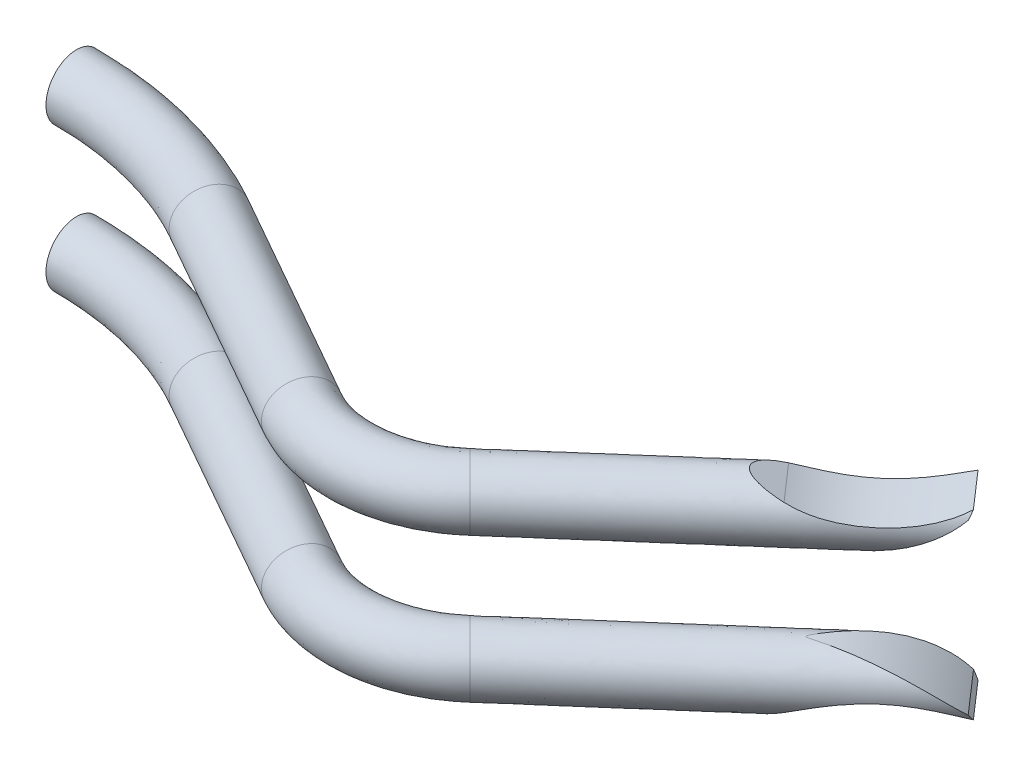
SolidWorks part; units mm, degrees
ref_plane "Front Plane" through (0, 0, 0) normal (0, 0, 1) x (1, 0, 0)
ref_plane "Top Plane" through (0, 0, 0) normal (0, 1, 0) x (1, 0, 0)
ref_plane "Right Plane" through (0, 0, 0) normal (1, 0, 0) x (0, 0, -1)
sketch "linear trace" plane through (0, 0, 0) normal (0, 1, 0) x (1, 0, 0)
  line L0 (544, 1224) -> (2720, 1224) construction
  line L1 (58.6476, 31.614) -> (61.5916, 29.9464)
  line L2 (67.5367, 33.5179) -> (63.697, 30.1609)
  line L3 (56.1008, 32.2852) -> (31.8502, 32.2852)
  line L4 (31.8502, 32.2852) -> (11.5916, 32.2852)
  line L8 (11.5916, 32.2852) -> (-52.4084, 32.2852)
  line L9 (61.5916, 31.5379) -> (61.5916, 26.5009) construction
  line L10 (58.6476, 34.5776) -> (58.6476, 27.8816) construction
  line L11 (31.8502, 35.1699) -> (31.8502, 28.7738) construction
  line L12 (66.6219, 34.4328) -> (68.5343, 32.5203) construction
  line L13 (11.5916, 37.7013) -> (11.5916, 27.1178) construction
  line L14 (-20.4084, 37.7013) -> (-20.4084, 23.3633) construction
  line L15 (56.1008, 34.5776) -> (56.1008, 28.9762) construction
  line L16 (-52.4084, 37.7013) -> (-52.4084, 27.1178) construction
  line L17 (-72.6669, 32.2852) -> (-52.4084, 32.2852)
  line L18 (-72.6669, 35.1699) -> (-72.6669, 28.7738) construction
  line L19 (-96.9175, 32.2852) -> (-72.6669, 32.2852)
  line L20 (-96.9175, 34.5776) -> (-96.9175, 28.9762) construction
  arc A0 (61.5916, 29.9464) -> (63.697, 30.1609) centre (62.4931, 31.5379) ccw
  arc A1 (56.1008, 32.2852) -> (58.6476, 31.614) centre (56.1008, 27.1178) cw
  point P27 (-20.4084, 32.2852)
ref_plane "Plane1" through (61.5916, 0, 0) normal (1, 0, 0) x (0, 0, -1)
ref_plane "Plane2" through (58.6476, 0, 0) normal (1, 0, 0) x (0, 0, -1)
ref_plane "Plane3" through (31.8502, 0, 0) normal (1, 0, 0) x (0, 0, -1)
ref_plane "Plane4" through (50.5273, 0, -50.5273) normal (0.7071, 0, -0.7071) x (0.7071, 0, 0.7071)
sketch "Sketch2" plane through (50.5273, 0, -50.5273) normal (0.7071, 0, -0.7071) x (0.7071, 0, 0.7071)
  circle A0 centre (24.0549, 0) radius 0.425
  point P4 (24.0549, 0)
  dimension "D1" = 0.85
sketch "Sketch3" plane through (61.5916, 0, 0) normal (1, 0, 0) x (0, 0, -1)
  circle A0 centre (29.9464, 0) radius 0.5
  dimension "D1" = 1
sketch "Sketch4" plane through (0, 0, 0) normal (0, 1, 0) x (1, 0, 0)
  line L2 (67.5367, 33.5179) -> (63.697, 30.1609) construction
  line L3 (67.5367, 33.5179) -> (63.697, 30.1609)
  line L4 (58.6476, 31.614) -> (61.5916, 29.9464) construction
  line L5 (58.6476, 31.614) -> (61.5916, 29.9464)
  arc A0 (61.5916, 29.9464) -> (63.697, 30.1609) centre (62.4931, 31.5379) ccw construction
  arc A1 (61.5916, 29.9464) -> (63.697, 30.1609) centre (62.4931, 31.5379) ccw
  arc A2 (58.6476, 31.614) -> (56.1008, 32.2852) centre (56.1008, 27.1178) ccw construction
  arc A3 (58.6476, 31.614) -> (56.1008, 32.2852) centre (56.1008, 27.1178) ccw
sweep "Sweep4" add profiles "Sketch2" path "Sketch4"
sketch "Sketch6" plane through (0, 0, 0) normal (0, 1, 0) x (1, 0, 0)
  line L0 (56.1008, 32.2852) -> (31.8502, 32.2852) construction
  line L1 (56.1008, 32.2852) -> (31.8502, 32.2852)
  line L2 (56.1008, 32.2852) -> (56.1008, 31.7852)
  line L3 (31.8502, 35.1699) -> (31.8502, 28.7738) construction
  line L4 (31.8502, 35.1699) -> (31.8502, 28.7738) construction
  line L5 (31.8502, 31.0852) -> (56.1008, 31.7852)
  line L6 (31.8502, 31.0852) -> (31.8502, 30.4852)
  line L7 (31.8502, 30.4852) -> (11.5916, 30.2852)
  line L8 (11.5916, 30.2852) -> (11.5916, 29.7852)
  line L9 (11.5916, 29.7852) -> (-52.4084, 29.7852)
  line L11 (11.5916, 32.2852) -> (-52.4084, 32.2852) construction
  line L15 (31.8502, 32.2852) -> (11.5916, 32.2852) construction
  line L17 (11.5916, 32.2852) -> (-52.4084, 32.2852)
  line L18 (-20.4084, 32.2852) -> (-20.4084, 29.7852) construction
  line L19 (31.8502, 32.2852) -> (11.5916, 32.2852)
  line L20 (11.5916, 32.2852) -> (11.5916, 27.6338) construction
  line L21 (-20.4084, 37.7013) -> (-20.4084, 23.3633) construction
  line L22 (-52.4084, 32.2852) -> (-52.4084, 27.6338) construction
  line L23 (-72.6669, 35.1699) -> (-72.6669, 28.7738) construction
  line L24 (-72.6669, 32.2852) -> (-52.4084, 32.2852)
  line L25 (-52.4084, 30.2852) -> (-52.4084, 29.7852)
  line L26 (-72.6669, 30.4852) -> (-52.4084, 30.2852)
  line L27 (-72.6669, 31.0852) -> (-72.6669, 30.4852)
  line L28 (-72.6669, 31.0852) -> (-96.9175, 31.7852)
  line L29 (-96.9175, 32.2852) -> (-96.9175, 31.7852)
  line L30 (-96.9175, 32.2852) -> (-72.6669, 32.2852)
  dimension "D1" = 0.5
  dimension "D2" = 1.2
  dimension "D3" = 2
  dimension "D4" = 1.8
  dimension "D5" = 2.5
revolve "Revolve1" [suppressed] add sketch "Sketch6" angle 360 about L8
ref_plane "Plane5" through (12.6499, 0, 14.4689) normal (-0.6582, 0, -0.7528) x (-0.7528, 0, 0.6582)
ref_plane "Plane6" through (12.979, 0, 14.8453) normal (-0.6582, 0, -0.7528) x (-0.7528, 0, 0.6582)
sketch "Sketch7" plane through (12.979, 0, 14.8453) normal (-0.6582, 0, -0.7528) x (-0.7528, 0, 0.6582)
  line L0 (804.1764, 1008.5492) -> (2890.5681, 390.5318) construction
  line L1 (-70.9069, -0.2587) -> (-70.4249, -0.4803)
  line L2 (-72.7165, -0.1669) -> (-72.7639, -0.2587)
  line L3 (-71.0972, 0.425) -> (-67.8057, 0.425) construction
  line L4 (-71.0972, 0.425) -> (-73.643, 0.425)
  line L5 (-73.643, 0.425) -> (-73.1771, -0.8091)
  line L6 (-73.1771, -0.8091) -> (-70.4249, -0.4803)
  line L7 (-67.8057, 0.425) -> (-72.906, 0.425) construction
  line L8 (-67.8057, 0.425) -> (-73.643, 0.425) construction
  arc A0 (-72.7639, -0.2587) -> (-70.9069, -0.2587) centre (-71.8354, -2.2779) cw
  arc A1 (-71.0972, 0.425) -> (-72.7165, -0.1669) centre (-71.0491, -2.2176) ccw
extrude "Cut-Extrude2" cut sketch "Sketch7" along normal blind 10
ref_plane "Plane7" through (0, 1, 0) normal (0, 1, 0) x (1, 0, 0)
mirror "Mirror1" about plane through (0, 1, 0) normal (0, 1, 0) of bodies 108
